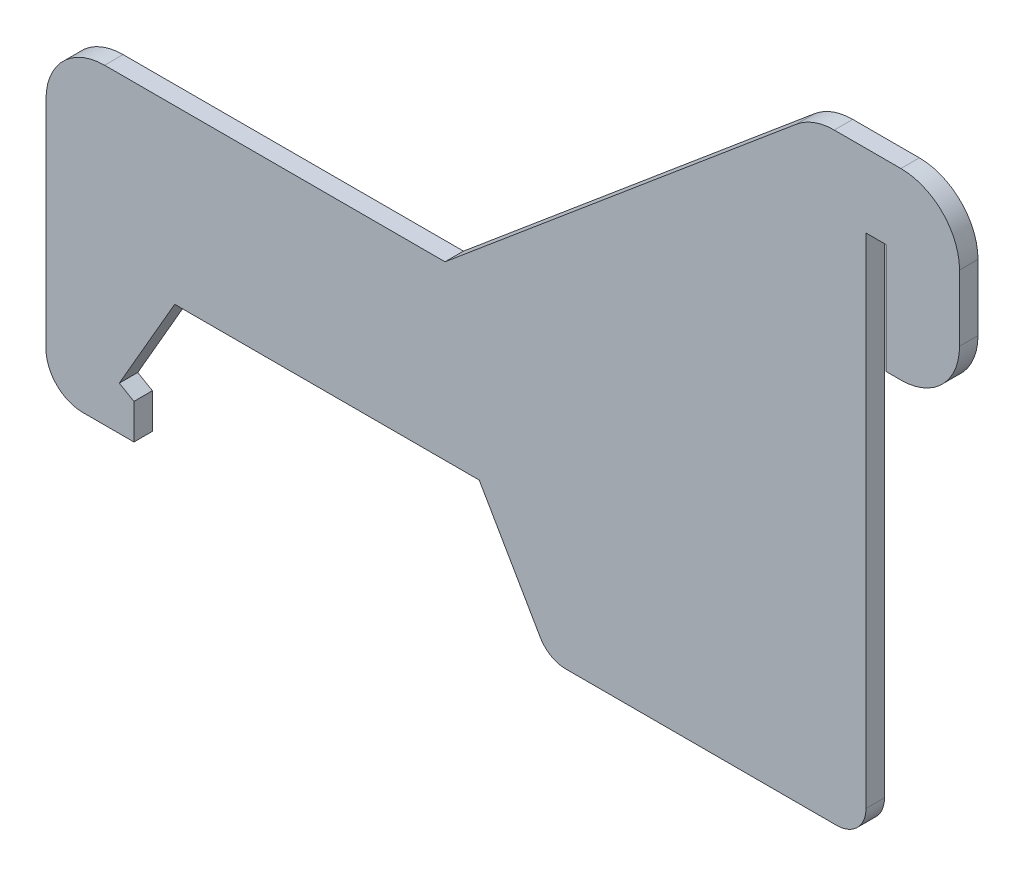
SolidWorks part; units mm, degrees
ref_plane "Front" through (0, 0, 0) normal (0, 0, 1) x (1, 0, 0)
ref_plane "Top" through (0, 0, 0) normal (0, 1, 0) x (1, 0, 0)
ref_plane "Right" through (0, 0, 0) normal (1, 0, 0) x (0, 0, -1)
sketch "Sketch1" plane through (0, 0, 0) normal (0, 0, 1) x (1, 0, 0)
  line L2 (27.2508, 1.2954) -> (21.9655, 10.4498)
  line L3 (21.9655, 10.4498) -> (-4.4185, 10.4498)
  line L4 (-4.4185, 10.4498) -> (-9.2204, 2.1326)
  line L5 (29.21, 8.7988) -> (33.8134, 0.8255) construction
  line L6 (-2.6384, 2.5853) -> (0.949, 8.7988) construction
  line L10 (20.0444, 10.3736) -> (-2.4974, 10.3736) construction
  line L11 (-7.9504, 1.3994) -> (-9.2204, 2.1326)
  line L12 (-8.9004, 2.5345) -> (-7.5146, 1.7344) construction
  line L14 (-7.9504, -1.651) -> (-12.3954, -1.651)
  line L15 (-15.5704, 1.524) -> (-15.5704, 20.2692)
  line L16 (-10.4904, 25.3492) -> (19.0013, 25.3492)
  line L17 (53.8988, -0.0508) -> (28.8932, -0.0508) construction
  line L18 (57.2262, 36.2204) -> (57.2262, 45.7454)
  line L19 (57.2262, 45.7454) -> (55.4736, 45.7454)
  line L20 (-8.9004, 2.5345) -> (-5.313, 8.748) construction
  line L21 (-7.9504, -1.651) -> (-7.9504, 1.3994)
  line L22 (33.02, -1.651) -> (0, -1.651) construction
  line L23 (22.86, 8.748) -> (27.4634, 0.7747) construction
  line L24 (55.4736, 45.7454) -> (55.4736, 2.5654)
  line L25 (19.0013, 25.3492) -> (49.4598, 50.9069)
  line L26 (52.7252, 52.0954) -> (58.4962, 52.0954)
  line L27 (63.5762, 47.0154) -> (63.5762, 41.3004)
  line L28 (58.4962, 36.2204) -> (57.2262, 36.2204)
  line L29 (29.4505, 0.0254) -> (52.9336, 0.0254)
  line L30 (57.15, 1.6002) -> (57.15, 44.0817) construction
  line L31 (57.15, 45.6692) -> (55.5498, 45.6692) construction
  line L32 (55.5498, 1.6002) -> (55.5498, 44.0817) construction
  arc A0 (-12.3954, -1.651) -> (-15.5704, 1.524) centre (-12.3954, 1.524) cw
  arc A1 (-15.5704, 20.2692) -> (-10.4904, 25.3492) centre (-10.4904, 20.2692) cw
  arc A2 (55.4736, 2.5654) -> (52.9336, 0.0254) centre (52.9336, 2.5654) cw
  arc A3 (63.5762, 41.3004) -> (58.4962, 36.2204) centre (58.4962, 41.3004) cw
  arc A4 (49.4598, 50.9069) -> (52.7252, 52.0954) centre (52.7252, 47.0154) cw
  arc A5 (29.4505, 0.0254) -> (27.2508, 1.2954) centre (29.4505, 2.5654) cw
  arc A7 (58.4962, 52.0954) -> (63.5762, 47.0154) centre (58.4962, 47.0154) cw
  point P51 (50.8762, 52.0954)
  point P54 (63.5762, 52.0954)
  dimension "D14" = 5.08
  dimension "D15" = 6.35
  dimension "D16" = 2.54
  dimension "D17" = 0.0762
  dimension "D18" = 6.35
  dimension "D19" = 3.175
  dimension "D22" = 2.54
  dimension "D23" = 5.08
  dimension "D3" = 0.508
  dimension "D4" = 0.0762
  dimension "D5" = 0.0762
  dimension "D6" = 25.4
  dimension "D7" = 0.0762
  dimension "D8" = 6.35
  dimension "D9" = 0.0762
  dimension "D10" = 7.62
  dimension "D11" = 0.0762
  dimension "D12" = 0.0762
  dimension "D13" = 9.525
  dimension "D20" = 140
  dimension "D21" = 12.7
extrude "Boss-Extrude1" add sketch "Sketch1" along normal mid plane 1.6002
